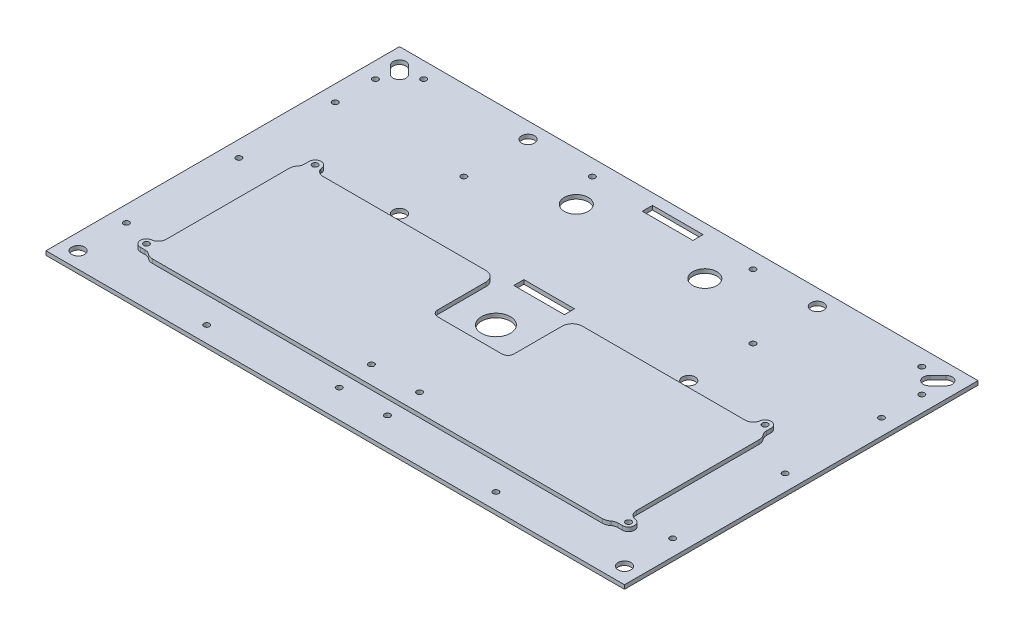
SolidWorks part; units mm, degrees
ref_plane "Front Plane" through (0, 0, 0) normal (0, 0, 1) x (1, 0, 0)
ref_plane "Top Plane" through (0, 0, 0) normal (0, 1, 0) x (1, 0, 0)
ref_plane "Right Plane" through (0, 0, 0) normal (1, 0, 0) x (0, 0, -1)
sketch "Sketch1" plane through (0, 0, 0) normal (0, 1, 0) x (1, 0, 0)
  line L1 (228.6, -139.7) -> (-228.6, -139.7)
  line L2 (228.6, -139.7) -> (228.6, 139.7)
  line L3 (228.6, 139.7) -> (-228.6, 139.7)
  line L4 (-228.6, -139.7) -> (-228.6, 139.7)
  line L5 (228.6, -139.7) -> (-228.6, 139.7) construction
  line L6 (228.6, 139.7) -> (-228.6, -139.7) construction
  point P0 (0, 0)
  dimension "D1" = 279.4
  dimension "D2" = 457.2
extrude "Boss-Extrude1" add sketch "Sketch1" along normal blind 3.175
sketch "Sketch2" plane through (0, 3.175, 0) normal (0, 1, 0) x (1, 0, 0)
  line L0 (-228.6, 139.7) -> (-228.6, -139.7) construction
  line L1 (228.6, 139.7) -> (-228.6, 139.7) construction
  line L2 (0, 0) -> (0, 139.7) construction
  line L3 (-212.3079, 130.5921) -> (-205.9579, 124.2421)
  line L4 (-219.4921, 123.4079) -> (-213.1421, 117.0579)
  line L5 (212.3079, 130.5921) -> (205.9579, 124.2421)
  line L6 (219.4921, 123.4079) -> (213.1421, 117.0579)
  line L9 (-20, 131) -> (-12, 131)
  line L10 (-20, 131) -> (-20, 123)
  line L11 (-20, 123) -> (-12, 123)
  line L12 (-12, 131) -> (-12, 123)
  line L13 (12, 131) -> (12, 123)
  line L14 (20, 123) -> (12, 123)
  line L15 (20, 131) -> (20, 123)
  line L16 (20, 131) -> (12, 131)
  line L17 (0, 76.2) -> (228.6, 76.2) construction
  line L18 (228.6, -139.7) -> (228.6, 139.7) construction
  line L19 (20, 21.4) -> (12, 21.4)
  line L20 (20, 21.4) -> (20, 29.4)
  line L21 (20, 29.4) -> (12, 29.4)
  line L22 (12, 21.4) -> (12, 29.4)
  line L23 (-12, 21.4) -> (-12, 29.4)
  line L24 (-20, 29.4) -> (-12, 29.4)
  line L25 (-20, 21.4) -> (-20, 29.4)
  line L26 (-20, 21.4) -> (-12, 21.4)
  circle A0 centre (-215.9, 127) radius 2.5 construction
  circle A1 centre (-209.55, 120.65) radius 2.5 construction
  arc A3 (-212.3079, 130.5921) -> (-219.4921, 123.4079) centre (-215.9, 127) ccw
  arc A4 (-213.1421, 117.0579) -> (-205.9579, 124.2421) centre (-209.55, 120.65) ccw
  arc A5 (213.1421, 117.0579) -> (205.9579, 124.2421) centre (209.55, 120.65) cw
  arc A6 (212.3079, 130.5921) -> (219.4921, 123.4079) centre (215.9, 127) cw
  circle A7 centre (-114.3, 127) radius 5.08
  circle A8 centre (114.3, 127) radius 5.08
  circle A9 centre (-215.9, -127) radius 5.08
  circle A10 centre (215.9, -127) radius 5.08
  circle A11 centre (114.3, 25.4) radius 5.08
  circle A12 centre (-114.3, 25.4) radius 5.08
  circle A13 centre (0, -12.7) radius 11.43
  point P32 (-20, 127)
  point P33 (-16, 131)
  point P38 (16, 131)
  point P39 (20, 127)
  point P56 (20, 25.4)
  point P57 (16, 21.4)
  point P58 (-16, 21.4)
  point P59 (-20, 25.4)
  dimension "D1" = 5
  dimension "D6" = 10.16
  dimension "D13" = 22.86
  dimension "D2" = 12.7
  dimension "D3" = 12.7
  dimension "D4" = 19.05
  dimension "D5" = 19.05
  dimension "D7" = 101.6
  dimension "D8" = 254
  dimension "D9" = 8
  dimension "D10" = 12.7
  dimension "D11" = 16
  dimension "D14" = 12.7
  dimension "D12" = 50.8
extrude "Cut-Extrude1" cut sketch "Sketch2" against normal blind 3.175
sketch "Sketch3" plane through (0, 3.175, 0) normal (0, 1, 0) x (1, 0, 0)
  line L1 (-20, 131) -> (20, 131)
  line L2 (-20, 131) -> (-20, 123)
  line L3 (-20, 123) -> (20, 123)
  line L4 (20, 131) -> (20, 123)
  line L5 (-20, 29.4) -> (20, 29.4)
  line L6 (-20, 29.4) -> (-20, 21.4)
  line L7 (-20, 21.4) -> (20, 21.4)
  line L8 (20, 29.4) -> (20, 21.4)
extrude "Cut-Extrude2" cut sketch "Sketch3" against normal blind 25.4
sketch "Sketch4" plane through (0, 3.175, 0) normal (0, 1, 0) x (1, 0, 0)
  line L0 (0, 0) -> (0, 139.7) construction
  line L1 (228.6, 139.7) -> (-228.6, 139.7) construction
  line L2 (-228.6, 139.7) -> (-228.6, -139.7) construction
  circle A0 centre (-196.85, 127) radius 2.25
  circle A1 centre (-215.9, 107.95) radius 2.25
  circle A2 centre (196.85, 127) radius 2.25
  circle A3 centre (215.9, 107.95) radius 2.25
  dimension "D3" = 4.5
  dimension "D1" = 12.7
  dimension "D2" = 31.75
  dimension "D4" = 12.7
  dimension "D5" = 31.75
extrude "Cut-Extrude3" cut sketch "Sketch4" against normal blind 25.4
sketch "Sketch5" plane through (0, 3.175, 0) normal (0, 1, 0) x (1, 0, 0)
  line L0 (228.6, 139.7) -> (-228.6, 139.7) construction
  line L1 (0, 139.7) -> (0, 29.4) construction
  line L2 (20, 29.4) -> (-20, 29.4) construction
  circle A0 centre (-50.8, 101.6) radius 9.525
  circle A1 centre (50.8, 101.6) radius 9.525
  dimension "D1" = 19.05
  dimension "D3" = 50.8
  dimension "D2" = 38.1
extrude "Cut-Extrude4" cut sketch "Sketch5" against normal blind 101.6
sketch "Sketch6" plane through (0, 3.175, 0) normal (0, 1, 0) x (1, 0, 0)
  line L0 (0, 139.7) -> (0, -139.7) construction
  line L1 (228.6, 139.7) -> (-228.6, 139.7) construction
  line L2 (-228.6, -139.7) -> (228.6, -139.7) construction
  line L3 (-228.6, 139.7) -> (-228.6, -139.7) construction
  line L4 (-114.3, 132.08) -> (-114.3, -139.7) construction
  circle A0 centre (-215.9, 76.2) radius 2.25
  circle A1 centre (-215.9, 0) radius 2.25
  circle A2 centre (-215.9, -88.9) radius 2.25
  circle A7 centre (-114.3, 127) radius 5.08 construction
  circle A8 centre (-114.3, -76.2) radius 2.25
  circle A10 centre (-114.3, 76.2) radius 2.25
  circle A11 centre (-63.5, 127) radius 2.25
  circle A12 centre (63.5, 127) radius 2.25
  circle A13 centre (114.3, 76.2) radius 2.25
  circle A14 centre (215.9, -88.9) radius 2.25
  circle A15 centre (215.9, 0) radius 2.25
  circle A16 centre (215.9, 76.2) radius 2.25
  dimension "D1" = 4.5
  dimension "D2" = 4.5
  dimension "D3" = 4.5
  dimension "D7" = 4.5
  dimension "D8" = 4.5
  dimension "D9" = 4.5
  dimension "D10" = 63.5
  dimension "D11" = 63.5
  dimension "D4" = 12.7
  dimension "D5" = 12.7
  dimension "D6" = 12.7
  dimension "D12" = 12.7
  dimension "D13" = 50.8
  dimension "D14" = 139.7
  dimension "D15" = 63.5
  dimension "D16" = 63.5
extrude "Cut-Extrude5" cut sketch "Sketch6" against normal blind 637.032
sketch "Sketch7" plane through (0, 3.175, 0) normal (0, 1, 0) x (1, 0, 0)
  line L0 (0, -104.775) -> (0, -139.7) construction
  line L1 (95.25, -104.775) -> (-95.25, -104.775)
  line L2 (95.25, -104.775) -> (95.25, -34.925)
  line L3 (95.25, -34.925) -> (-95.25, -34.925)
  line L4 (-95.25, -104.775) -> (-95.25, -34.925)
  line L5 (95.25, -104.775) -> (-95.25, -34.925) construction
  line L6 (95.25, -34.925) -> (-95.25, -104.775) construction
  line L7 (-95.25, -34.925) -> (-31.75, -34.925)
  line L8 (-95.25, -34.925) -> (-95.25, 15.875)
  line L9 (-95.25, 15.875) -> (-31.75, 15.875)
  line L10 (-31.75, -34.925) -> (-31.75, 15.875)
  line L11 (95.25, -34.925) -> (31.75, -34.925)
  line L12 (95.25, -34.925) -> (95.25, 15.875)
  line L13 (95.25, 15.875) -> (31.75, 15.875)
  line L14 (31.75, -34.925) -> (31.75, 15.875)
  line L15 (-95.25, 15.875) -> (-184.15, 15.875)
  line L16 (-95.25, 15.875) -> (-95.25, -104.775)
  line L17 (-95.25, -104.775) -> (-184.15, -104.775)
  line L18 (-184.15, 15.875) -> (-184.15, -104.775)
  line L19 (95.25, 15.875) -> (184.15, 15.875)
  line L20 (95.25, 15.875) -> (95.25, -104.775)
  line L21 (95.25, -104.775) -> (184.15, -104.775)
  line L22 (184.15, 15.875) -> (184.15, -104.775)
  line L23 (-228.6, -139.7) -> (228.6, -139.7) construction
  circle A0 centre (19.05, -117.475) radius 2.25
  circle A1 centre (-19.05, -117.475) radius 2.25
  circle A2 centre (-114.3, -127) radius 2.25
  circle A3 centre (-215.9, -127) radius 5.08 construction
  circle A4 centre (-215.9, -127) radius 5.08
  circle A5 centre (-114.3, -76.2) radius 2.25 construction
  circle A6 centre (-114.3, -76.2) radius 2.25
  circle A7 centre (114.3, -127) radius 2.25
  circle A8 centre (-177.8, 22.225) radius 2.25
  circle A11 centre (-190.5, -98.425) radius 2.25
  circle A12 centre (190.5, -98.425) radius 2.25
  circle A13 centre (177.8, 22.225) radius 2.25
  point P0 (0, -69.85)
  circle M8 centre (-114.3, -76.2) radius 2.25
  dimension "D9" = 4.5
  dimension "D1" = 190.5
  dimension "D2" = 69.85
  dimension "D3" = 69.85
  dimension "D4" = 50.8
  dimension "D5" = 63.5
  dimension "D6" = 88.9
  dimension "D7" = 19.05
  dimension "D8" = 12.7
  dimension "D10" = 6.35
  dimension "D11" = 6.35
  dimension "D12" = 6.35
  dimension "D13" = 6.35
extrude "Cut-Extrude6" cut sketch "Sketch7" against normal blind 25.4 contours L4 L1 L2 L3 | L3 L10 L9 L8 | L14 L3 L12 L13 | L15 L18 L17 L4 L8 M8 | L22 L19 L12 L2 L21 | A1 | A0 | A7 | A11 | A8 | A12 | A2 | A13
fillet "Fillet1" radius 6.35 8 edges at (-184.15, 1.5875, 104.775) (184.15, 1.5875, 104.775) (184.15, 1.5875, -15.875) (31.75, 1.5875, -15.875) (31.75, 1.5875, 34.925) (-31.75, 1.5875, 34.925) (-31.75, 1.5875, -15.875) (-184.15, 1.5875, -15.875)
sketch "Sketch8" plane through (0, 3.175, 0) normal (0, 1, 0) x (1, 0, 0)
  line L76 (177.8, -104.775) -> (-177.8, -104.775) construction
  line L84 (-30.1625, -28.575) -> (-30.1625, 9.525)
  line L85 (25.4, -33.3375) -> (-25.4, -33.3375)
  line L86 (30.1625, 9.525) -> (30.1625, -28.575)
  line L87 (177.8, 17.4625) -> (38.1, 17.4625)
  line L88 (185.7375, -98.425) -> (185.7375, 9.525)
  line L89 (-177.8, -106.3625) -> (177.8, -106.3625)
  line L90 (-185.7375, 9.525) -> (-185.7375, -98.425)
  line L91 (-38.1, 17.4625) -> (-177.8, 17.4625)
  line L92 (-30.1625, -28.575) -> (-30.1625, 9.525)
  line L93 (25.4, -33.3375) -> (-25.4, -33.3375)
  line L94 (30.1625, 9.525) -> (30.1625, -28.575)
  line L95 (177.8, 17.4625) -> (38.1, 17.4625)
  line L96 (185.7375, -98.425) -> (185.7375, 9.525)
  line L97 (-177.8, -106.3625) -> (177.8, -106.3625)
  line L98 (-185.7375, 9.525) -> (-185.7375, -98.425)
  line L99 (-38.1, 17.4625) -> (-177.8, 17.4625)
  circle A63 centre (-19.05, -92.075) radius 2.25
  circle A64 centre (19.05, -92.075) radius 2.25
  circle A65 centre (19.05, -117.475) radius 2.25 construction
  circle A66 centre (-19.05, -117.475) radius 2.25 construction
  circle A67 centre (19.05, -117.475) radius 2.25
  circle A68 centre (-19.05, -117.475) radius 2.25
  arc A71 (-30.1625, 9.525) -> (-38.1, 17.4625) centre (-38.1, 9.525) ccw
  arc A72 (-30.1625, -28.575) -> (-25.4, -33.3375) centre (-25.4, -28.575) ccw
  arc A73 (25.4, -33.3375) -> (30.1625, -28.575) centre (25.4, -28.575) ccw
  arc A74 (38.1, 17.4625) -> (30.1625, 9.525) centre (38.1, 9.525) ccw
  arc A75 (185.7375, 9.525) -> (177.8, 17.4625) centre (177.8, 9.525) ccw
  arc A76 (177.8, -106.3625) -> (185.7375, -98.425) centre (177.8, -98.425) ccw
  arc A77 (-185.7375, -98.425) -> (-177.8, -106.3625) centre (-177.8, -98.425) ccw
  arc A78 (-177.8, 17.4625) -> (-185.7375, 9.525) centre (-177.8, 9.525) ccw
  arc A79 (-30.1625, 9.525) -> (-38.1, 17.4625) centre (-38.1, 9.525) ccw
  arc A80 (-30.1625, -28.575) -> (-25.4, -33.3375) centre (-25.4, -28.575) ccw
  arc A81 (25.4, -33.3375) -> (30.1625, -28.575) centre (25.4, -28.575) ccw
  arc A82 (38.1, 17.4625) -> (30.1625, 9.525) centre (38.1, 9.525) ccw
  arc A83 (185.7375, 9.525) -> (177.8, 17.4625) centre (177.8, 9.525) ccw
  arc A84 (177.8, -106.3625) -> (185.7375, -98.425) centre (177.8, -98.425) ccw
  arc A85 (-185.7375, -98.425) -> (-177.8, -106.3625) centre (-177.8, -98.425) ccw
  arc A86 (-177.8, 17.4625) -> (-185.7375, 9.525) centre (-177.8, 9.525) ccw
  point P10 (0, 0)
  point P11 (0, 0)
  point P12 (0, 0)
  dimension "D2" = 12.7
  dimension "D1" = 1.5875
extrude "Boss-Extrude2" add sketch "Sketch8" along normal blind 3.175 separate body contours L99 A86 L98 A85 L97 A84 L96 A83 L95 A82 L94 A81 L93 A80 L92 A79 A63 A64
sketch "Sketch9" plane through (0, 6.35, 0) normal (0, 1, 0) x (1, 0, 0)
  line L1 (-182.5625, 22.225) -> (-182.5625, 18.5053)
  line L2 (0, -33.3375) -> (0, -106.3625) construction
  line L4 (-190.5, -103.1875) -> (-186.7803, -103.1875)
  line L5 (190.5, -103.1875) -> (186.7803, -103.1875)
  line L6 (182.5625, 22.225) -> (182.5625, 18.5053)
  line L8 (-38.1, 17.4625) -> (-177.8, 17.4625)
  line L9 (-185.7375, 9.525) -> (-185.7375, -98.425)
  line L10 (-177.8, -106.3625) -> (177.8, -106.3625)
  line L11 (185.7375, -98.425) -> (185.7375, 9.525)
  line L12 (177.8, 17.4625) -> (38.1, 17.4625)
  line L13 (30.1625, 9.525) -> (30.1625, -28.575)
  line L14 (25.4, -33.3375) -> (-25.4, -33.3375)
  line L15 (-30.1625, -28.575) -> (-30.1625, 9.525)
  line L16 (-38.1, 17.4625) -> (-166.8891, 17.4625)
  line L17 (-185.7375, 9.525) -> (-185.7375, -87.5141)
  line L18 (-177.8, -106.3625) -> (177.8, -106.3625)
  line L19 (185.7375, -87.5141) -> (185.7375, 9.525)
  line L20 (166.8891, 17.4625) -> (38.1, 17.4625)
  line L21 (30.1625, 9.525) -> (30.1625, -28.575)
  line L22 (25.4, -33.3375) -> (-25.4, -33.3375)
  line L23 (-30.1625, -28.575) -> (-30.1625, 9.525)
  circle A0 centre (-177.8, 22.225) radius 2.25 construction
  circle A1 centre (-177.8, 22.225) radius 2.25
  circle A2 centre (-190.5, -98.425) radius 2.25 construction
  circle A3 centre (-190.5, -98.425) radius 2.25
  circle A4 centre (177.8, 22.225) radius 2.25 construction
  circle A5 centre (177.8, 22.225) radius 2.25
  circle A6 centre (190.5, -98.425) radius 2.25 construction
  circle A7 centre (190.5, -98.425) radius 2.25
  arc A8 (-30.1625, 9.525) -> (-38.1, 17.4625) centre (-38.1, 9.525) ccw
  arc A9 (-177.8, 17.4625) -> (-185.7375, 9.525) centre (-177.8, 9.525) ccw
  arc A10 (-185.7375, -98.425) -> (-177.8, -106.3625) centre (-177.8, -98.425) ccw
  arc A11 (177.8, -106.3625) -> (185.7375, -98.425) centre (177.8, -98.425) ccw
  arc A12 (185.7375, 9.525) -> (177.8, 17.4625) centre (177.8, 9.525) ccw
  arc A13 (38.1, 17.4625) -> (30.1625, 9.525) centre (38.1, 9.525) ccw
  arc A14 (25.4, -33.3375) -> (30.1625, -28.575) centre (25.4, -28.575) ccw
  arc A15 (-30.1625, -28.575) -> (-25.4, -33.3375) centre (-25.4, -28.575) ccw
  arc A16 (-30.1625, 9.525) -> (-38.1, 17.4625) centre (-38.1, 9.525) ccw
  arc A17 (-183.9736, 14.514) -> (-185.7375, 9.525) centre (-177.8, 9.525) ccw
  arc A18 (-182.789, -104.5986) -> (-177.8, -106.3625) centre (-177.8, -98.425) ccw
  arc A19 (177.8, -106.3625) -> (182.789, -104.5986) centre (177.8, -98.425) ccw
  arc A20 (185.7375, 9.525) -> (183.9736, 14.514) centre (177.8, 9.525) ccw
  arc A21 (38.1, 17.4625) -> (30.1625, 9.525) centre (38.1, 9.525) ccw
  arc A22 (25.4, -33.3375) -> (30.1625, -28.575) centre (25.4, -28.575) ccw
  arc A23 (-30.1625, -28.575) -> (-25.4, -33.3375) centre (-25.4, -28.575) ccw
  arc A24 (-173.0375, 22.225) -> (-182.5625, 22.225) centre (-177.8, 22.225) ccw
  arc A25 (-190.5, -93.6625) -> (-190.5, -103.1875) centre (-190.5, -98.425) ccw
  arc A26 (182.5625, 22.225) -> (173.0375, 22.225) centre (177.8, 22.225) ccw
  arc A27 (190.5, -103.1875) -> (190.5, -93.6625) centre (190.5, -98.425) ccw
  arc A28 (-173.0375, 22.225) -> (-166.8891, 17.4625) centre (-166.8891, 23.8125) ccw
  arc A29 (-182.5625, 18.5053) -> (-183.9736, 14.514) centre (-188.9125, 18.5053) cw
  arc A30 (-186.7803, -103.1875) -> (-182.789, -104.5986) centre (-186.7803, -109.5375) cw
  arc A31 (-190.5, -93.6625) -> (-185.7375, -87.5141) centre (-192.0875, -87.5141) ccw
  arc A32 (186.7803, -103.1875) -> (182.789, -104.5986) centre (186.7803, -109.5375) ccw
  arc A33 (190.5, -93.6625) -> (185.7375, -87.5141) centre (192.0875, -87.5141) cw
  arc A34 (190.5, -93.6625) -> (190.5, -103.1875) centre (190.5, -98.425) cw
  arc A35 (173.0375, 22.225) -> (166.8891, 17.4625) centre (166.8891, 23.8125) cw
  arc A36 (182.5625, 18.5053) -> (183.9736, 14.514) centre (188.9125, 18.5053) ccw
  arc A37 (173.0375, 22.225) -> (182.5625, 22.225) centre (177.8, 22.225) cw
  circle A38 centre (19.05, -92.075) radius 2.25 construction
  circle A39 centre (-19.05, -92.075) radius 2.25 construction
  circle A40 centre (19.05, -92.075) radius 2.25
  circle A41 centre (-19.05, -92.075) radius 2.25
  point P49 (0, 0)
  dimension "D2" = 6.35
  dimension "D3" = 6.35
  dimension "D1" = 0
extrude "Boss-Extrude3" add sketch "Sketch9" against normal blind 3.175 contours A1 | L2 L22 A23 L23 A16 L16 A28 A24 L1 A29 A17 L17 A31 A25 L4 A30 A18 L18 A3 A1 | L22 L2 L18 A19 A32 L5 A27 A33 L19 A20 A36 L6 A26 A35 L20 A21 L21 A22 A5 A7
